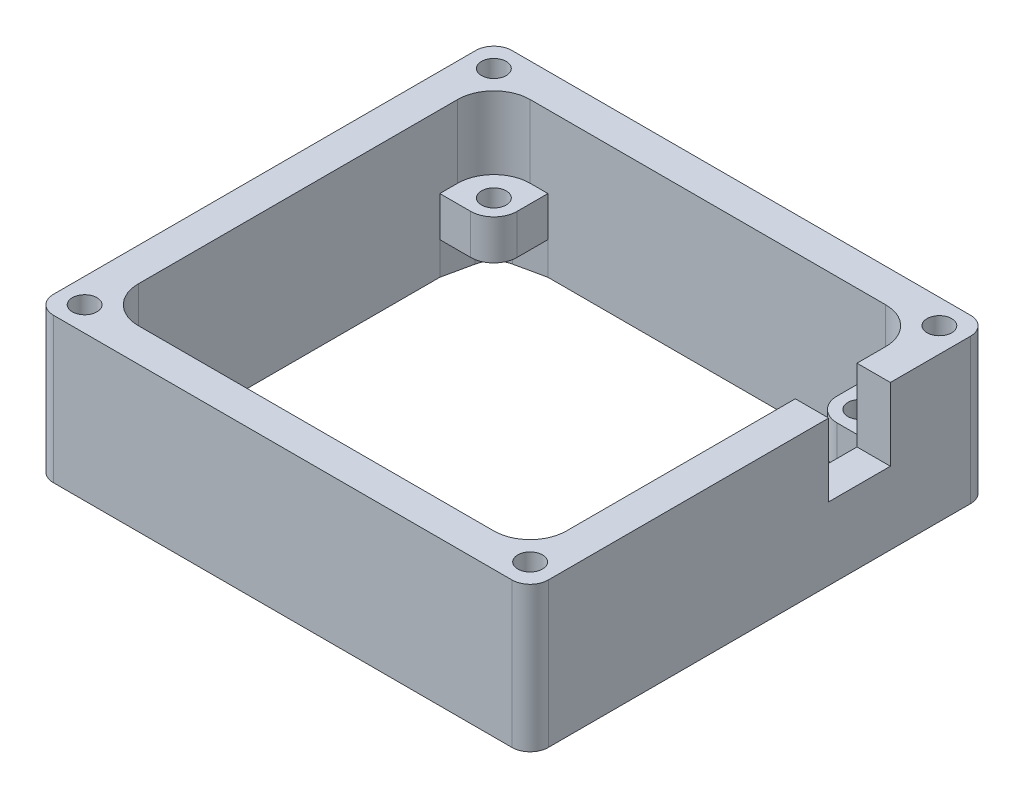
SolidWorks part; units mm, degrees
ref_plane "Front" through (0, 0, 0) normal (0, 0, 1) x (1, 0, 0)
ref_plane "Top" through (0, 0, 0) normal (0, 1, 0) x (1, 0, 0)
ref_plane "Right" through (0, 0, 0) normal (1, 0, 0) x (0, 0, -1)
sketch "ｽｹｯﾁ1" plane through (0, 0, 0) normal (0, 1, 0) x (1, 0, 0)
  line L0 (31.6, 31.6) -> (-31.6, 31.6)
  line L1 (24.5, 27) -> (-24.5, 27)
  line L2 (29.5, 22) -> (29.5, -22)
  line L3 (24.5, -27) -> (-24.5, -27)
  line L4 (-29.5, 22) -> (-29.5, -22)
  line L5 (29.5, 27) -> (-29.5, -27) construction
  line L6 (29.5, -27) -> (-29.5, 27) construction
  line L7 (-34.1, 29.1) -> (-34.1, -29.1)
  line L8 (31.6, -31.6) -> (-31.6, -31.6)
  line L9 (34.1, 29.1) -> (34.1, -29.1)
  line L10 (34.1, 31.6) -> (-34.1, 31.6) construction
  line L11 (34.1, 31.6) -> (34.1, -31.6) construction
  line L12 (34.1, -31.6) -> (-34.1, -31.6) construction
  line L13 (-34.1, 31.6) -> (-34.1, -31.6) construction
  line L14 (29.5, 27) -> (29.5, -27) construction
  line L15 (29.5, -27) -> (-29.5, -27) construction
  line L16 (-29.5, 27) -> (-29.5, -27) construction
  line L17 (29.5, 27) -> (-29.5, 27) construction
  arc A0 (31.6, 31.6) -> (34.1, 29.1) centre (31.6, 29.1) cw
  arc A1 (31.6, -31.6) -> (34.1, -29.1) centre (31.6, -29.1) ccw
  arc A2 (-34.1, -29.1) -> (-31.6, -31.6) centre (-31.6, -29.1) ccw
  arc A3 (-31.6, 31.6) -> (-34.1, 29.1) centre (-31.6, 29.1) ccw
  arc A4 (29.5, -22) -> (24.5, -27) centre (24.5, -22) cw
  arc A5 (-24.5, -27) -> (-29.5, -22) centre (-24.5, -22) cw
  arc A6 (-24.5, 27) -> (-29.5, 22) centre (-24.5, 22) ccw
  arc A7 (24.5, 27) -> (29.5, 22) centre (24.5, 22) cw
  point P0 (0, 0)
  dimension "D4" = 2.5
  dimension "D5" = 5
  dimension "D1" = 59
  dimension "D2" = 54
  dimension "D3" = 4.6
extrude "ﾎﾞｽ - 押し出し2" add sketch "ｽｹｯﾁ1" along normal blind 20
sketch "ｽｹｯﾁ2" plane through (0, 0, 0) normal (0, -1, 0) x (1, 0, 0)
  line L8 (34.1, -29.1) -> (34.1, 29.1)
  line L9 (31.6, 31.6) -> (-31.6, 31.6)
  line L10 (-34.1, 29.1) -> (-34.1, -29.1)
  line L11 (-31.6, -31.6) -> (31.6, -31.6)
  line L12 (34.1, -29.1) -> (34.1, 29.1)
  line L13 (31.6, 31.6) -> (-31.6, 31.6)
  line L14 (-34.1, 29.1) -> (-34.1, -29.1)
  line L15 (-31.6, -31.6) -> (31.6, -31.6)
  arc A8 (31.6, -31.6) -> (34.1, -29.1) centre (31.6, -29.1) ccw
  arc A9 (34.1, 29.1) -> (31.6, 31.6) centre (31.6, 29.1) ccw
  arc A10 (-31.6, 31.6) -> (-34.1, 29.1) centre (-31.6, 29.1) ccw
  arc A11 (-34.1, -29.1) -> (-31.6, -31.6) centre (-31.6, -29.1) ccw
  arc A12 (31.6, -31.6) -> (34.1, -29.1) centre (31.6, -29.1) ccw
  arc A13 (34.1, 29.1) -> (31.6, 31.6) centre (31.6, 29.1) ccw
  arc A14 (-31.6, 31.6) -> (-34.1, 29.1) centre (-31.6, 29.1) ccw
  arc A15 (-34.1, -29.1) -> (-31.6, -31.6) centre (-31.6, -29.1) ccw
  dimension "D1" = 0
extrude "ﾎﾞｽ - 押し出し3" add sketch "ｽｹｯﾁ2" along normal blind 4
sketch "ｽｹｯﾁ3" plane through (0, 0, 0) normal (0, 1, 0) x (1, 0, 0)
  line L0 (-25.25, -22.75) -> (25.25, -22.75)
  line L1 (25.25, -22.75) -> (25.25, 22.75)
  line L2 (25.25, 22.75) -> (-25.25, 22.75)
  line L3 (-25.25, 22.75) -> (-25.25, -22.75)
  line L4 (29.5, 19.55) -> (22.05, 19.55)
  line L5 (29.5, -22) -> (29.5, 22) construction
  line L6 (22.05, 19.55) -> (22.05, 27)
  line L7 (24.5, 27) -> (-24.5, 27) construction
  line L8 (-29.5, 19.55) -> (-22.05, 19.55)
  line L9 (-29.5, 22) -> (-29.5, -22) construction
  line L10 (-22.05, 19.55) -> (-22.05, 27)
  line L11 (29.5, -19.55) -> (22.05, -19.55)
  line L12 (22.05, -19.55) -> (22.05, -27)
  line L13 (-22.05, -27) -> (-22.05, -19.55)
  line L14 (-24.5, -27) -> (24.5, -27) construction
  line L15 (-22.05, -19.55) -> (-29.5, -19.55)
  circle A0 centre (-25.25, 22.75) radius 1.7
  circle A1 centre (25.25, 22.75) radius 1.7
  circle A2 centre (-25.25, -22.75) radius 1.7
  circle A3 centre (25.25, -22.75) radius 1.7
  circle A4 centre (-25.25, 22.75) radius 3.2
  circle A5 centre (-25.25, -22.75) radius 3.2
  circle A6 centre (25.25, -22.75) radius 3.2
  circle A7 centre (25.25, 22.75) radius 3.2
  point P8 (0, -22.75)
  point P9 (-25.25, 0)
  line M7 (29.5, -22) -> (29.5, 22)
  line M8 (24.5, 27) -> (-24.5, 27)
  line M9 (-29.5, 22) -> (-29.5, -22)
  line M10 (-24.5, -27) -> (24.5, -27)
  arc M17 (-29.5, -22) -> (-24.5, -27) centre (-24.5, -22) ccw
  arc M18 (24.5, -27) -> (29.5, -22) centre (24.5, -22) ccw
  arc M19 (29.5, 22) -> (24.5, 27) centre (24.5, 22) ccw
  arc M20 (-24.5, 27) -> (-29.5, 22) centre (-24.5, 22) ccw
  dimension "D3" = 3.4
  dimension "D1" = 50.5
  dimension "D2" = 45.5
  dimension "D4" = 1.5
extrude "ﾎﾞｽ - 押し出し4" add sketch "ｽｹｯﾁ3" along normal blind 10 contours L2 A7 L1 A1 | L1 A7 L2 A1 | L2 A4 L3 A0 | L3 A4 L2 A0 | L3 A5 L0 A2 | L0 A5 L3 A2 | L0 A6 L1 A3 | L1 A6 L0 A3 | A6 L12 L11 M10 M18 M7 | A7 L4 L6 M7 M19 M8 | A5 L15 L13 M9 M17 M10 | A4 L10 L8 M8 M20 M9
sketch "ｽｹｯﾁ4" plane through (0, 20, 0) normal (0, 1, 0) x (1, 0, 0)
  line L0 (28.0355, -25.5355) -> (33.3678, -30.8678)
  line L1 (33.3678, 30.8678) -> (28.0355, 25.5355)
  line L2 (-28.0355, 25.5355) -> (-33.3678, 30.8678)
  line L3 (-33.3678, -30.8678) -> (-28.0355, -25.5355)
  circle A0 centre (30.7017, 28.2017) radius 1.7
  circle A1 centre (-30.7017, 28.2017) radius 1.7
  circle A2 centre (-30.7017, -28.2017) radius 1.7
  circle A3 centre (30.7017, -28.2017) radius 1.7
  arc A6 (31.6, -31.6) -> (34.1, -29.1) centre (31.6, -29.1) ccw construction
  arc A7 (24.5, -27) -> (29.5, -22) centre (24.5, -22) ccw construction
  arc A8 (34.1, 29.1) -> (31.6, 31.6) centre (31.6, 29.1) ccw construction
  arc A9 (29.5, 22) -> (24.5, 27) centre (24.5, 22) ccw construction
  arc A10 (-24.5, 27) -> (-29.5, 22) centre (-24.5, 22) ccw construction
  arc A11 (-31.6, 31.6) -> (-34.1, 29.1) centre (-31.6, 29.1) ccw construction
  arc A12 (-34.1, -29.1) -> (-31.6, -31.6) centre (-31.6, -29.1) ccw construction
  arc A13 (-29.5, -22) -> (-24.5, -27) centre (-24.5, -22) ccw construction
  point P16 (30.7017, -28.2017)
  point P41 (-30.7017, -28.2017)
  point P42 (-30.7017, 28.2017)
  point P43 (30.7017, 28.2017)
  dimension "D1" = 3.4
extrude "ｶｯﾄ - 押し出し1" cut sketch "ｽｹｯﾁ4" against normal through all contours L3 A2 | L3 A2 | L2 A1 | L2 A1 | L1 A0 | L1 A0 | L0 A3 | L0 A3
sketch "ｽｹｯﾁ5" plane through (0, 20, 0) normal (0, 1, 0) x (1, 0, 0)
  line L0 (29.5, -22) -> (29.5, 22) construction
  line L1 (29.5, 18.05) -> (34.1, 18.05)
  line L2 (29.5, 18.05) -> (29.5, 9.55)
  line L3 (29.5, 9.55) -> (34.1, 9.55)
  line L4 (34.1, 18.05) -> (34.1, 9.55)
  line L5 (34.1, -29.1) -> (34.1, 29.1) construction
  circle A0 centre (25.25, 22.75) radius 1.7 construction
  dimension "D1" = 4.7
  dimension "D2" = 8.5
extrude "ｶｯﾄ - 押し出し2" cut sketch "ｽｹｯﾁ5" against normal up to vertex (10 mm away)
sketch "ｽｹｯﾁ6" plane through (0, -4, 0) normal (0, -1, 0) x (1, 0, 0)
  line L8 (34.1, -29.1) -> (34.1, 29.1)
  line L9 (31.6, 31.6) -> (-31.6, 31.6)
  line L10 (-34.1, 29.1) -> (-34.1, -29.1)
  line L11 (-31.6, -31.6) -> (31.6, -31.6)
  line L12 (34.1, -29.1) -> (34.1, 29.1)
  line L13 (31.6, 31.6) -> (-31.6, 31.6)
  line L14 (-34.1, 29.1) -> (-34.1, -29.1)
  line L15 (-31.6, -31.6) -> (31.6, -31.6)
  arc A8 (31.6, -31.6) -> (34.1, -29.1) centre (31.6, -29.1) ccw
  arc A9 (34.1, 29.1) -> (31.6, 31.6) centre (31.6, 29.1) ccw
  arc A10 (-31.6, 31.6) -> (-34.1, 29.1) centre (-31.6, 29.1) ccw
  arc A11 (-34.1, -29.1) -> (-31.6, -31.6) centre (-31.6, -29.1) ccw
  arc A12 (31.6, -31.6) -> (34.1, -29.1) centre (31.6, -29.1) ccw
  arc A13 (34.1, 29.1) -> (31.6, 31.6) centre (31.6, 29.1) ccw
  arc A14 (-31.6, 31.6) -> (-34.1, 29.1) centre (-31.6, 29.1) ccw
  arc A15 (-34.1, -29.1) -> (-31.6, -31.6) centre (-31.6, -29.1) ccw
  dimension "D1" = 0
extrude "ｶｯﾄ - 押し出し3" cut sketch "ｽｹｯﾁ6" against normal up to vertex (4 mm away)
sketch "ｽｹｯﾁ7" plane through (0, 0, 0) normal (0, -1, 0) x (1, 0, 0)
  line L0 (-29.5, -19.55) -> (-28.6333, -23.5655)
  line L1 (-26.0655, -26.1333) -> (-22.05, -27)
  line L2 (29.5, -19.55) -> (28.6333, -23.5655)
  line L3 (26.0655, -26.1333) -> (22.05, -27)
  line L4 (29.5, 19.55) -> (28.6333, 23.5655)
  line L5 (26.0655, 26.1333) -> (22.05, 27)
  line L6 (-29.5, 19.55) -> (-28.6333, 23.5655)
  line L7 (-26.0655, 26.1333) -> (-22.05, 27)
  line L8 (-33.3678, 30.8678) -> (-22.9873, 20.4873) construction
  line L9 (-33.3678, -30.8678) -> (-22.9873, -20.4873) construction
  line L10 (33.3678, -30.8678) -> (22.9873, -20.4873) construction
  line L11 (22.9873, 20.4873) -> (33.3678, 30.8678) construction
  arc A0 (-31.6, 31.6) -> (-34.1, 29.1) centre (-31.6, 29.1) ccw construction
  arc A1 (-25.25, 19.55) -> (-22.05, 22.75) centre (-25.25, 22.75) ccw construction
  arc A2 (-34.1, -29.1) -> (-31.6, -31.6) centre (-31.6, -29.1) ccw construction
  arc A3 (-22.05, -22.75) -> (-25.25, -19.55) centre (-25.25, -22.75) ccw construction
  arc A4 (31.6, -31.6) -> (34.1, -29.1) centre (31.6, -29.1) ccw construction
  arc A5 (25.25, -19.55) -> (22.05, -22.75) centre (25.25, -22.75) ccw construction
  arc A6 (22.05, 22.75) -> (25.25, 19.55) centre (25.25, 22.75) ccw construction
  arc A7 (34.1, 29.1) -> (31.6, 31.6) centre (31.6, 29.1) ccw construction
  arc A8 (28.6333, -23.5655) -> (26.0655, -26.1333) centre (25.3587, -22.8587) cw
  arc A9 (28.6333, 23.5655) -> (26.0655, 26.1333) centre (25.3587, 22.8587) ccw
  arc A10 (-28.6333, 23.5655) -> (-26.0655, 26.1333) centre (-25.3587, 22.8587) cw
  arc A11 (-28.6333, -23.5655) -> (-26.0655, -26.1333) centre (-25.3587, -22.8587) ccw
  point P21 (-28.1775, 25.6775)
  point P53 (28.1775, 25.6775)
  point P54 (28.1775, -25.6775)
  point P55 (-28.1775, -25.6775)
  point P58 (28.1775, -25.6775)
  point P61 (28.1775, 25.6775)
  point P64 (-28.1775, 25.6775)
  point P67 (-28.1775, -25.6775)
  arc M3 (-22.05, -22.75) -> (-25.25, -19.55) centre (-25.25, -22.75) ccw
  line M4 (-25.25, -19.55) -> (-29.5, -19.55)
  line M6 (-29.5, 19.55) -> (-25.25, 19.55)
  arc M7 (-25.25, 19.55) -> (-22.05, 22.75) centre (-25.25, 22.75) ccw
  line M8 (-22.05, 22.75) -> (-22.05, 27)
  line M10 (22.05, 27) -> (22.05, 22.75)
  arc M11 (22.05, 22.75) -> (25.25, 19.55) centre (25.25, 22.75) ccw
  line M12 (25.25, 19.55) -> (29.5, 19.55)
  line M14 (29.5, -19.55) -> (25.25, -19.55)
  arc M15 (25.25, -19.55) -> (22.05, -22.75) centre (25.25, -22.75) ccw
  line M16 (22.05, -22.75) -> (22.05, -27)
  line M18 (-22.05, -27) -> (-22.05, -22.75)
  circle M31 centre (-25.25, -22.75) radius 1.7
  circle M32 centre (-25.25, 22.75) radius 1.7
  circle M33 centre (25.25, -22.75) radius 1.7
  circle M34 centre (25.25, 22.75) radius 1.7
  dimension "D1" = 3.35
extrude "ｶｯﾄ - 押し出し4" cut sketch "ｽｹｯﾁ7" against normal blind 4.5 contours A8 L2 L3 M14 M15 M16 M33 | L0 A11 L1 M18 M3 M4 M31 | A10 L6 L7 M6 M7 M8 M32 | L4 A9 L5 M10 M11 M12 M34
